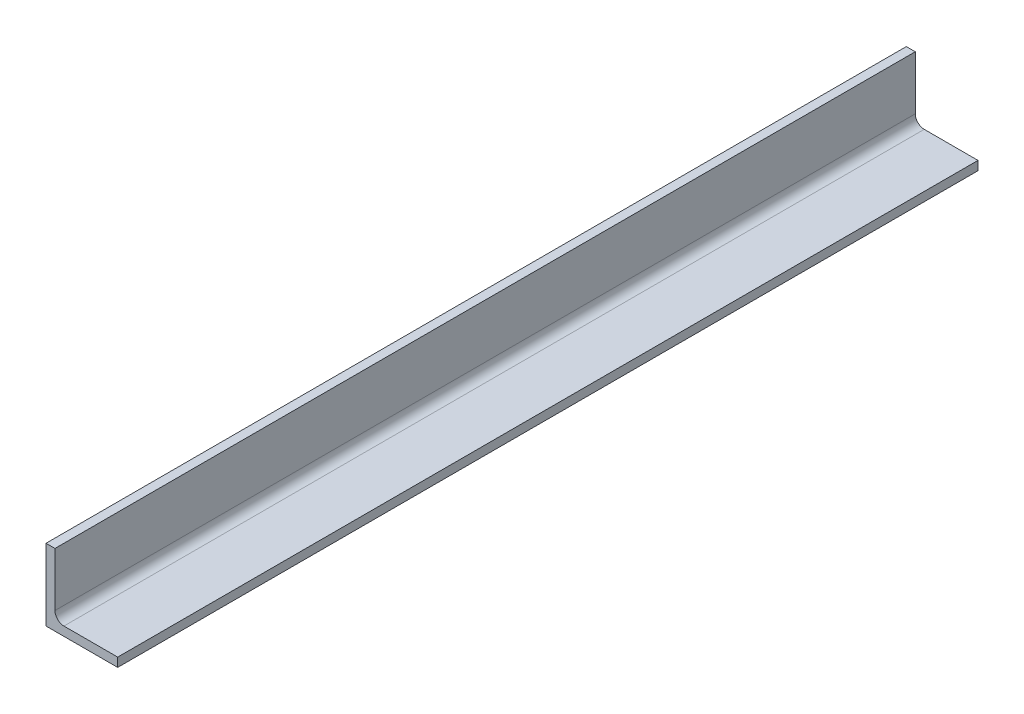
SolidWorks part; units mm, degrees
ref_plane "Front Plane" through (0, 0, 0) normal (0, 0, 1) x (1, 0, 0)
ref_plane "Top Plane" through (0, 0, 0) normal (0, 1, 0) x (1, 0, 0)
ref_plane "Right Plane" through (0, 0, 0) normal (1, 0, 0) x (0, 0, -1)
sketch "Sketch2" plane through (0, 0, 0) normal (0, 0, 1) x (1, 0, 0)
  line L0 (0, 0) -> (0, 50.8)
  line L1 (0, 50.8) -> (6.35, 50.8)
  line L2 (6.35, 50.8) -> (6.35, 12.7)
  line L3 (12.7, 6.35) -> (50.8, 6.35)
  line L4 (50.8, 6.35) -> (50.8, 0)
  line L5 (50.8, 0) -> (0, 0)
  arc A0 (12.7, 6.35) -> (6.35, 12.7) centre (12.7, 12.7) cw
  dimension "D4" = 6.35
  dimension "D1" = 6.35
  dimension "D2" = 50.8
  dimension "D3" = 50.8
extrude "Boss-Extrude1" add sketch "Sketch2" along normal mid plane 609.6
